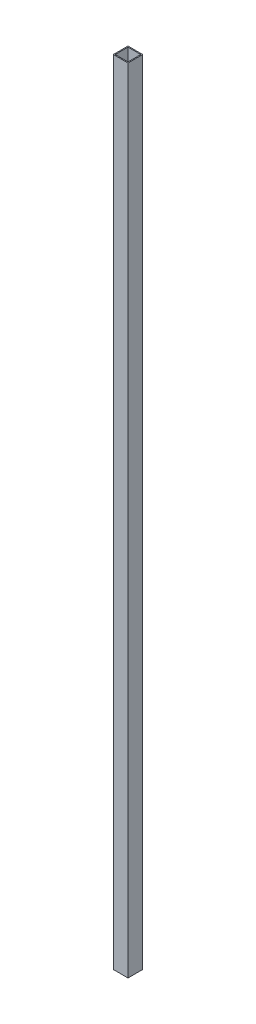
SolidWorks part; units mm, degrees
ref_plane "Front Plane" through (0, 0, 0) normal (0, 0, 1) x (1, 0, 0)
ref_plane "Top Plane" through (0, 0, 0) normal (0, 1, 0) x (1, 0, 0)
ref_plane "Right Plane" through (0, 0, 0) normal (1, 0, 0) x (0, 0, -1)
sketch "Sketch2" plane through (0, 0, 0) normal (0, 1, 0) x (1, 0, 0)
  line L1 (-15, 15) -> (15, 15)
  line L2 (-15, 15) -> (-15, -15)
  line L3 (-15, -15) -> (15, -15)
  line L4 (15, 15) -> (15, -15)
  line L5 (-15, 15) -> (15, -15) construction
  line L6 (-15, -15) -> (15, 15) construction
  line L10 (-13, 13) -> (-13, -13)
  line L11 (-13, -13) -> (13, -13)
  line L12 (13, 13) -> (13, -13)
  line L13 (-13, 13) -> (13, 13)
  point P0 (0, 0)
  dimension "D1" = 30
  dimension "D2" = 30
  dimension "D3" = 2
extrude "Boss-Extrude1" add sketch "Sketch2" along normal mid plane 1615
